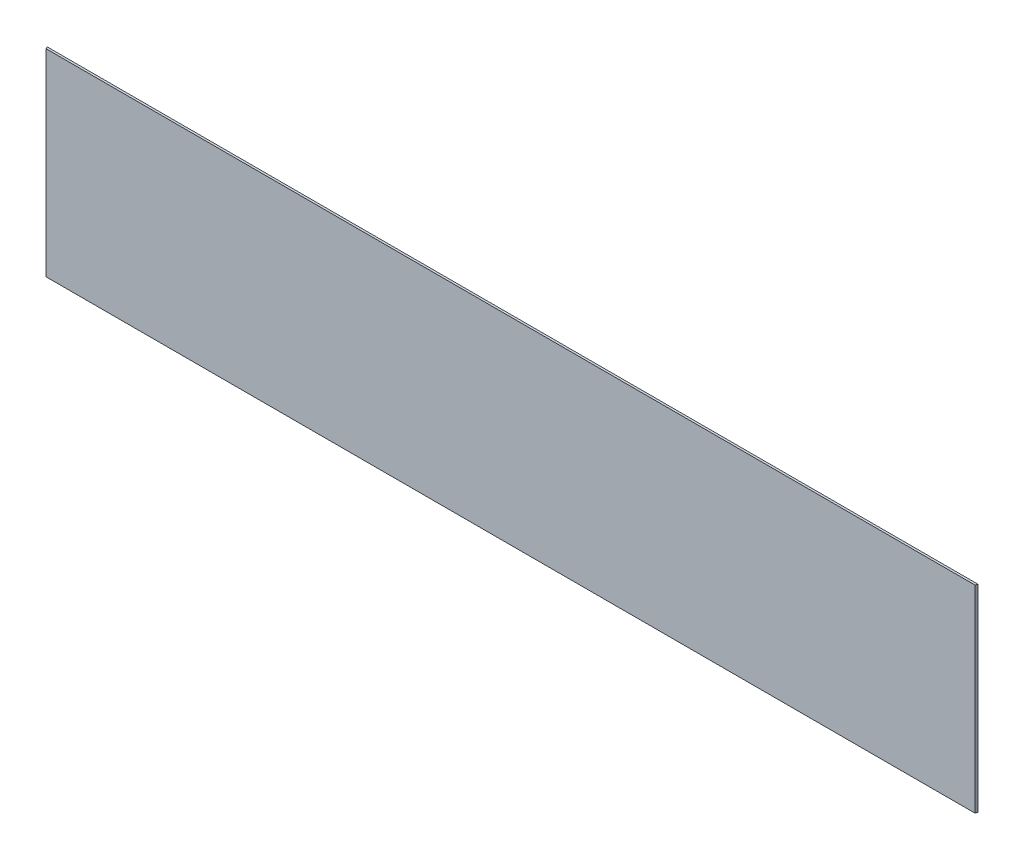
SolidWorks part; units mm, degrees
material "6061 Alloy"
ref_plane "Front Plane" through (0, 0, 0) normal (0, 0, 1) x (1, 0, 0)
ref_plane "Top Plane" through (0, 0, 0) normal (0, 1, 0) x (1, 0, 0)
ref_plane "Right Plane" through (0, 0, 0) normal (1, 0, 0) x (0, 0, -1)
sketch "Sketch1" plane through (0, 0, 0) normal (0, 1, 0) x (1, 0, 0)
  line L0 (673.1, 1.5875) -> (671.7849, -1.5875)
  line L1 (-673.1, 1.5875) -> (673.1, 1.5875)
  line L3 (-671.7849, -1.5875) -> (671.7849, -1.5875)
  line L5 (-673.1, 1.5875) -> (671.7862, -1.5844) construction
  line L6 (-671.7862, -1.5844) -> (673.1, 1.5875) construction
  line L7 (-673.1, 1.5875) -> (-671.7849, -1.5875)
  point P0 (0, 0)
  dimension "D1" = 1346.2
extrude "Extrude1" add sketch "Sketch1" along normal mid plane 285.75
